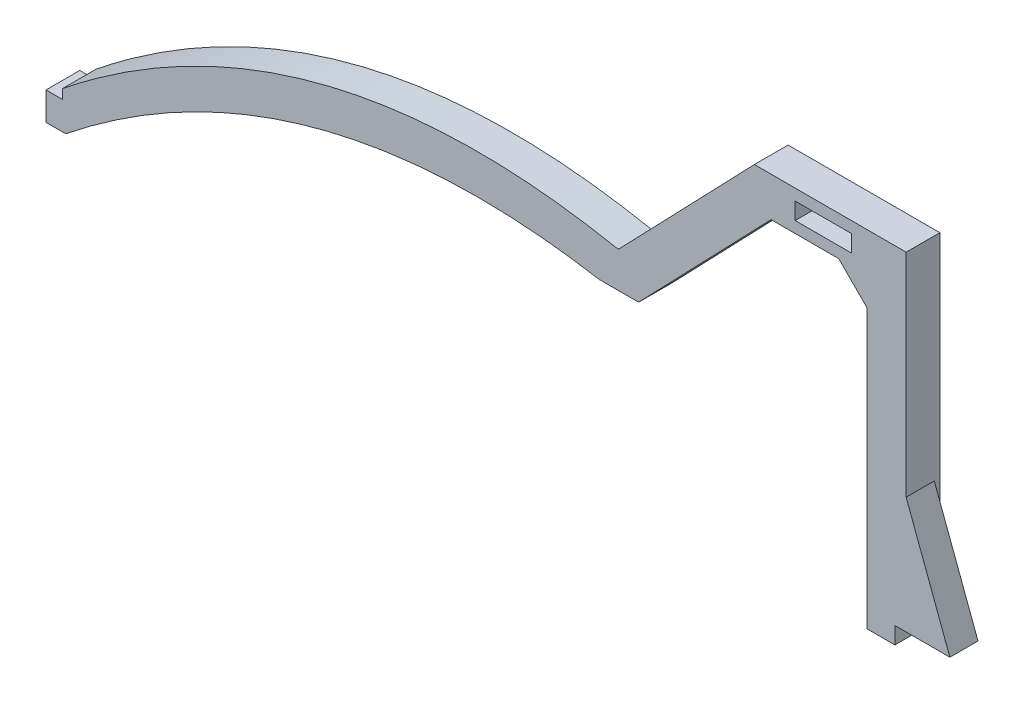
SolidWorks part; units mm, degrees
ref_plane "Front" through (0, 0, 0) normal (0, 0, 1) x (1, 0, 0)
ref_plane "Top" through (0, 0, 0) normal (0, 1, 0) x (1, 0, 0)
ref_plane "Right" through (0, 0, 0) normal (1, 0, 0) x (0, 0, -1)
sketch "Sketch1" plane through (0, 0, 0) normal (0, 0, 1) x (1, 0, 0)
  line L0 (0, -5) -> (100, -5) construction
  line L1 (-0.5335, 0) -> (-3.5, 0)
  line L2 (-0.5335, 1.7077) -> (-0.5335, 0)
  line L3 (0, -5) -> (-3.5, -5)
  line L4 (-3.5, 0) -> (-3.5, -5)
  line L5 (98.2958, 26.3469) -> (122.4894, 51.505)
  line L6 (122.4894, 51.505) -> (149.4894, 51.505)
  line L7 (147.4894, -10) -> (147.4894, -7)
  line L8 (94.9038, 20) -> (101.9038, 20)
  line L9 (101.9038, 20) -> (125.4693, 44.505)
  line L10 (125.4693, 44.505) -> (142.4894, 44.505)
  line L11 (142.4894, 44.505) -> (142.4894, -10)
  line L12 (147.4894, -7) -> (149.4894, -7)
  line L13 (149.4894, -7) -> (149.4894, 51.505)
  line L15 (142.4894, -10) -> (147.4894, -10)
  spline S0 degree 2 poles (0, -5) (42.6048, 29.0357) (94.9038, 20) knots 0 0 0 1 1 1
  spline S1 degree 3 poles (-0.5335, 1.7077) (28.7999, 25.1881) (61.7179, 33.5155) (98.0268, 26.4005) (98.2958, 26.3469) knots 0 0 0 0 1 1.007459 1.007459 1.007459 1.007459
  point P14 (98.4038, 20)
  point P21 (148.4894, -7)
  dimension "D6" = 101.3539
  dimension "D2" = 5
  dimension "D3" = 100
  dimension "D4" = 25
  dimension "D5" = 2
  dimension "D7" = 7
  dimension "D8" = 3
  dimension "D9" = 7
  dimension "D11" = 7
  dimension "D12" = 27
  dimension "D14" = 7
  dimension "D15" = 50
  dimension "D16" = 3.5
  dimension "D18" = 5
extrude "Boss-Extrude1" add sketch "Sketch1" along normal blind 6
sketch "Sketch2" plane through (0, 0, 6) normal (0, 0, 1) x (1, 0, 0)
  line L0 (149.4894, -7) -> (157.2675, -7)
  line L2 (157.2675, -7) -> (149.4894, 13.7638)
  line L3 (149.4894, -7) -> (149.4894, 51.505) construction
  line L5 (149.4894, 13.7638) -> (149.4894, -7)
extrude "Boss-Extrude2" add sketch "Sketch2" against normal blind 5
chamfer "Chamfer1" distance 5 angle 45 1 edges at (142.4894, 44.505, 3)
sketch "Sketch3" plane through (0, 0, 6) normal (0, 0, 1) x (1, 0, 0)
  line L0 (149.4894, 51.505) -> (122.4894, 51.505) construction
  line L1 (129.7487, 49.505) -> (139.7487, 49.505)
  line L2 (129.7487, 49.505) -> (129.7487, 46.505)
  line L3 (129.7487, 46.505) -> (139.7487, 46.505)
  line L4 (139.7487, 49.505) -> (139.7487, 46.505)
  dimension "D1" = 3
  dimension "D2" = 2
  dimension "D3" = 10
extrude "Cut-Extrude1" cut sketch "Sketch3" against normal blind 6
